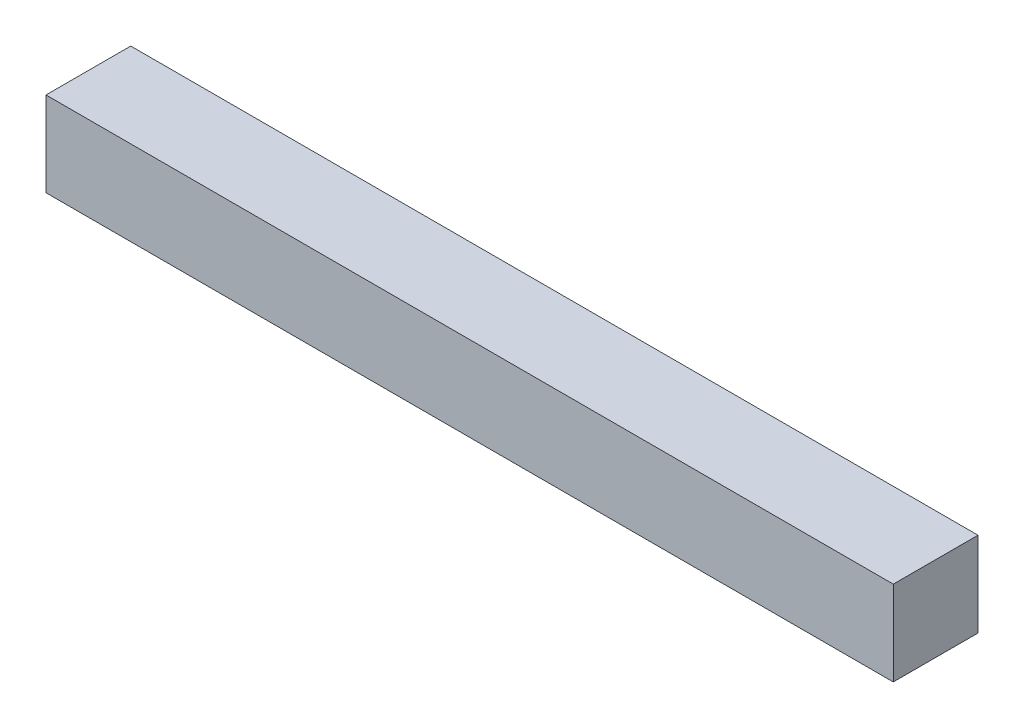
SolidWorks part; units mm, degrees
ref_plane "Front Plane" through (0, 0, 0) normal (0, 0, 1) x (1, 0, 0)
ref_plane "Top Plane" through (0, 0, 0) normal (0, 1, 0) x (1, 0, 0)
ref_plane "Right Plane" through (0, 0, 0) normal (1, 0, 0) x (0, 0, -1)
sketch "Sketch1" plane through (0, 0, 0) normal (0, 1, 0) x (1, 0, 0)
  line L1 (-75, -7.5) -> (75, -7.5)
  line L2 (-75, -7.5) -> (-75, 7.5)
  line L3 (-75, 7.5) -> (75, 7.5)
  line L4 (75, -7.5) -> (75, 7.5)
  line L5 (-75, -7.5) -> (75, 7.5) construction
  line L6 (-75, 7.5) -> (75, -7.5) construction
  point P0 (0, 0)
  dimension "D1" = 150
  dimension "D2" = 15
extrude "Boss-Extrude1" add sketch "Sketch1" along normal blind 15
sketch "Sketch2" plane through (-75, 0, 0) normal (-1, 0, 0) x (0, 0, 1)
  line L0 (-7.5, 15) -> (7.5, 0) construction
  circle A0 centre (0, 7.5) radius 4.8125
  dimension "D1" = 9.625
extrude "Cut-Extrude1" cut sketch "Sketch2" against normal offset from surface (140 mm away) 10 up to face at (75, 7.5, 0)
